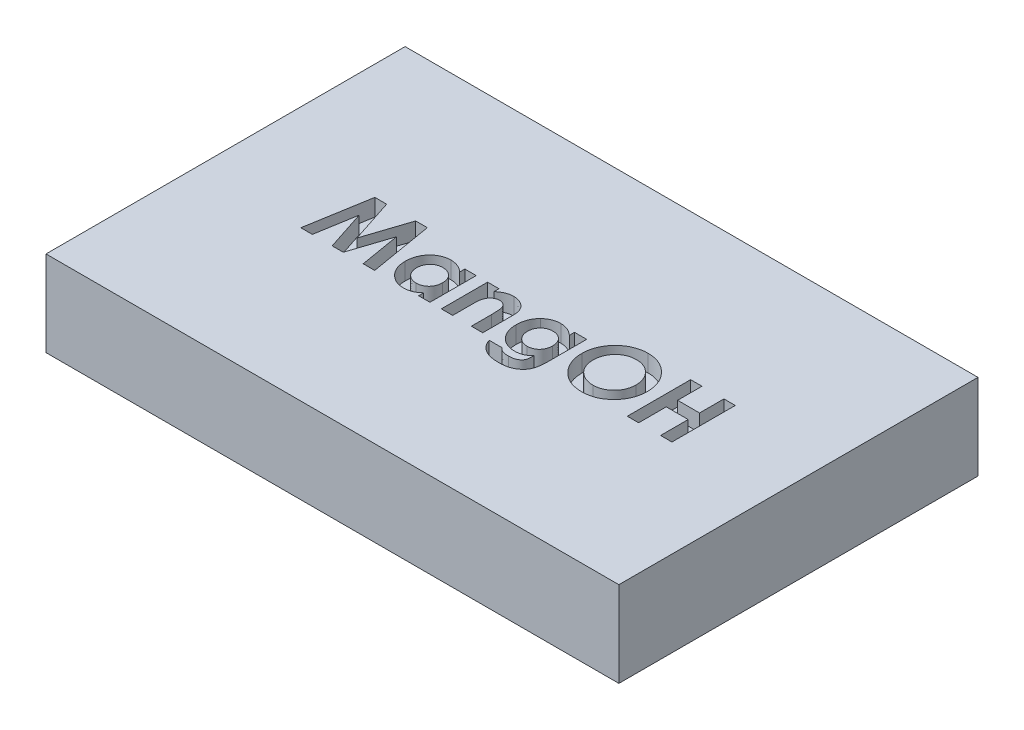
SolidWorks part; units mm, degrees
ref_plane "Front Plane" through (0, 0, 0) normal (0, 0, 1) x (1, 0, 0)
ref_plane "Top Plane" through (0, 0, 0) normal (0, 1, 0) x (1, 0, 0)
ref_plane "Right Plane" through (0, 0, 0) normal (1, 0, 0) x (0, 0, -1)
sketch "Sketch4" plane through (0, 0, 0) normal (0, 1, 0) x (1, 0, 0)
  line L1 (-33.5, -21) -> (33.5, -21)
  line L2 (-33.5, -21) -> (-33.5, 21)
  line L3 (-33.5, 21) -> (33.5, 21)
  line L4 (33.5, -21) -> (33.5, 21)
  line L5 (-33.5, -21) -> (33.5, 21) construction
  line L6 (-33.5, 21) -> (33.5, -21) construction
  point P0 (0, 0)
  dimension "D1" = 42
  dimension "D2" = 67
extrude "Boss-Extrude1" add sketch "Sketch4" along normal blind 10
sketch "Sketch5" plane through (0, 10, 0) normal (0, 1, 0) x (1, 0, 0)
  line L0 (0, 21) -> (0, -27.8961) construction
  line L1 (33.5, 21) -> (-33.5, 21) construction
  line L2 (-21.4414, -3.448) -> (22.5543, -3.448) construction
  text T0 "<b>MangOH Yellow</b>" font "Century Gothic" height in points 28
extrude "Cut-Extrude1" cut sketch "Sketch5" against normal blind 2
